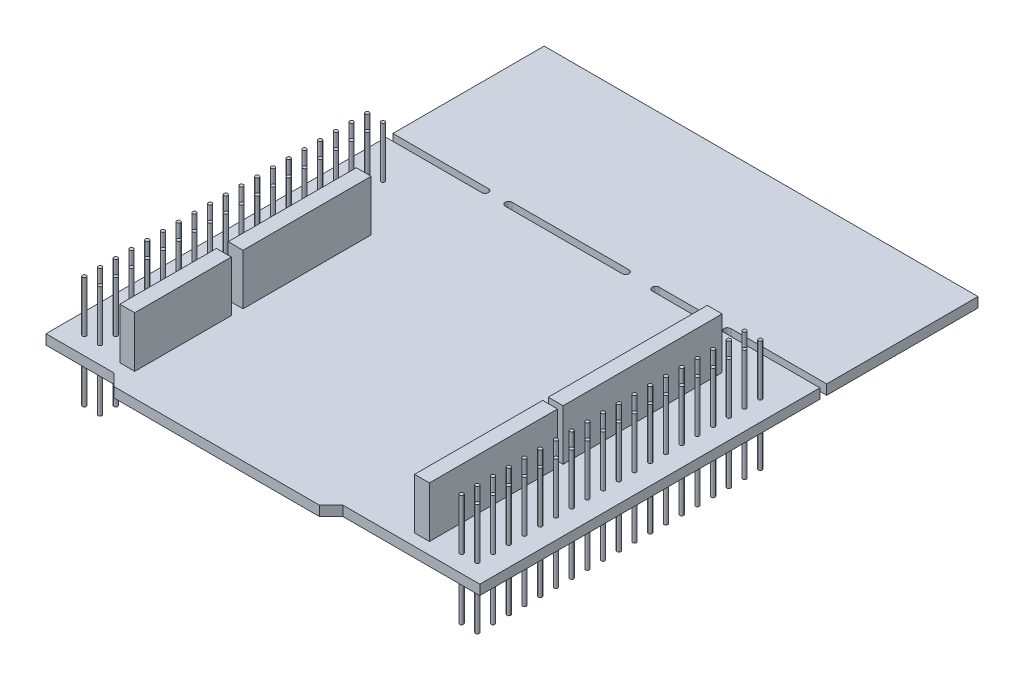
SolidWorks part; units mm, degrees
ref_plane "Front Plane" through (0, 0, 0) normal (0, 0, 1) x (1, 0, 0)
ref_plane "Top Plane" through (0, 0, 0) normal (0, 1, 0) x (1, 0, 0)
ref_plane "Right Plane" through (0, 0, 0) normal (1, 0, 0) x (0, 0, -1)
sketch "Sketch1" plane through (0, 0, 0) normal (0, 1, 0) x (1, 0, 0)
  line L0 (-24.05, -40.25) -> (-22.15, -42.15)
  line L1 (35.05, -40.25) -> (12.95, -40.25)
  line L2 (35.05, -40.25) -> (35.05, 40.25)
  line L3 (35.05, 40.25) -> (-35.05, 40.25)
  line L4 (-35.05, -40.25) -> (-35.05, 40.25)
  line L5 (35.05, -40.25) -> (-35.05, 40.25) construction
  line L6 (35.05, 40.25) -> (-35.05, -40.25) construction
  line L7 (-22.15, -42.15) -> (11.05, -42.15)
  line L8 (11.05, -42.15) -> (12.95, -40.25)
  line L9 (-24.05, -40.25) -> (-35.05, -40.25)
  line L10 (-35.05, 15.25) -> (-19.6, 15.25) construction
  line L11 (-35.05, 15.8) -> (-19.6, 15.8)
  line L12 (-35.05, 14.7) -> (-19.6, 14.7)
  line L13 (-15.8, 15.25) -> (3.1, 15.25) construction
  line L14 (-15.8, 15.8) -> (3.1, 15.8)
  line L15 (-15.8, 14.7) -> (3.1, 14.7)
  line L16 (7.95, 15.25) -> (15.15, 15.25) construction
  line L17 (7.95, 15.8) -> (15.15, 15.8)
  line L18 (7.95, 14.7) -> (15.15, 14.7)
  line L19 (19.55, 15.25) -> (35.05, 15.25) construction
  line L20 (19.55, 15.8) -> (35.05, 15.8)
  line L21 (19.55, 14.7) -> (35.05, 14.7)
  arc A0 (-35.05, 15.8) -> (-35.05, 14.7) centre (-35.05, 15.25) ccw
  arc A1 (-19.6, 14.7) -> (-19.6, 15.8) centre (-19.6, 15.25) ccw
  arc A2 (-15.8, 15.8) -> (-15.8, 14.7) centre (-15.8, 15.25) ccw
  arc A3 (3.1, 14.7) -> (3.1, 15.8) centre (3.1, 15.25) ccw
  arc A4 (7.95, 15.8) -> (7.95, 14.7) centre (7.95, 15.25) ccw
  arc A5 (15.15, 14.7) -> (15.15, 15.8) centre (15.15, 15.25) ccw
  arc A6 (19.55, 15.8) -> (19.55, 14.7) centre (19.55, 15.25) ccw
  arc A7 (35.05, 14.7) -> (35.05, 15.8) centre (35.05, 15.25) ccw
  point P0 (0, 0)
  point P12 (-27.325, 15.25)
  point P17 (-6.35, 15.25)
  point P24 (11.55, 15.25)
  point P31 (27.3, 15.25)
  dimension "D7" = 0.55
  dimension "D1" = 70.1
  dimension "D2" = 80.5
  dimension "D3" = 37
  dimension "D4" = 11
  dimension "D5" = 1.9
  dimension "D6" = 135
  dimension "D8" = 15.45
  dimension "D9" = 25
  dimension "D10" = 18.9
  dimension "D11" = 3.8
  dimension "D12" = 4.85
  dimension "D13" = 7.2
  dimension "D14" = 4.4
extrude "Boss-Extrude1" add sketch "Sketch1" along normal blind 1.6 contours A6 L20 L2 L3 L4 L11 A1 L12 L9 L0 L7 L8 L1 L21 A5 L18 A4 L17 A3 L15 A2 L14
sketch "Sketch2" plane through (0, 1.6, 0) normal (0, 1, 0) x (1, 0, 0)
  line L0 (-35.05, -40.25) -> (-35.05, 14.7) construction
  line L1 (-24.05, -40.25) -> (-35.05, -40.25) construction
  circle A0 centre (-31.75, -37.35) radius 0.3
  circle A1 centre (-29.21, -37.35) radius 0.3
  dimension "D1" = 0.6
  dimension "D2" = 2.54
  dimension "D3" = 5.84
  dimension "D4" = 2.9
extrude "Boss-Extrude2" add sketch "Sketch2" along normal blind 8.25
ref_plane "Plane1" through (0, 0.8, 0) normal (0, 1, 0) x (1, 0, 0)
pattern_linear "LPattern1" count 19 spacing 2.54 along (0, 0, -1) of "Boss-Extrude2"
mirror "Mirror1" about plane through (0, 0.8, 0) normal (0, 1, 0) of "LPattern1", "Boss-Extrude2" second plane through (0, 0, 0) second plane normal (1, 0, 0)
sketch "Sketch3" plane through (0, 1.6, 0) normal (0, 1, 0) x (1, 0, 0)
  line L0 (-24.05, -40.25) -> (-35.05, -40.25) construction
  line L1 (-25.01, -38.35) -> (-22.61, -38.35)
  line L2 (-25.01, -38.35) -> (-25.01, -22.75)
  line L3 (-25.01, -22.75) -> (-22.61, -22.75)
  line L4 (-22.61, -38.35) -> (-22.61, -22.75)
  line L5 (-25.01, -20.85) -> (-22.61, -20.85)
  line L6 (-25.01, -20.85) -> (-25.01, -0.15)
  line L7 (-25.01, -0.15) -> (-22.61, -0.15)
  line L8 (-22.61, -20.85) -> (-22.61, -0.15)
  line L9 (22.61, -38.35) -> (25.01, -38.35)
  line L10 (22.61, -38.35) -> (22.61, -17.65)
  line L11 (22.61, -17.65) -> (25.01, -17.65)
  line L12 (25.01, -38.35) -> (25.01, -17.65)
  line L13 (22.61, -16.75) -> (25.01, -16.75)
  line L14 (22.61, -16.75) -> (22.61, 8.95)
  line L15 (22.61, 8.95) -> (25.01, 8.95)
  line L16 (25.01, -16.75) -> (25.01, 8.95)
  line L17 (35.05, -40.25) -> (12.95, -40.25) construction
  circle A0 centre (-29.21, -37.35) radius 0.3 construction
  circle A1 centre (29.21, -37.35) radius 0.3 construction
  dimension "D1" = 2.4
  dimension "D2" = 15.6
  dimension "D3" = 1.9
  dimension "D4" = 20.7
  dimension "D5" = 4.2
  dimension "D6" = 1.9
  dimension "D7" = 4.2
  dimension "D8" = 1.9
  dimension "D9" = 20.7
  dimension "D10" = 0.9
  dimension "D11" = 25.7
extrude "Boss-Extrude3" add sketch "Sketch3" along normal blind 8.2
equation "\"D7@Sketch3\"=\"D5@Sketch3\""
equation "\"D8@Sketch3\"=\"D6@Sketch3\""
